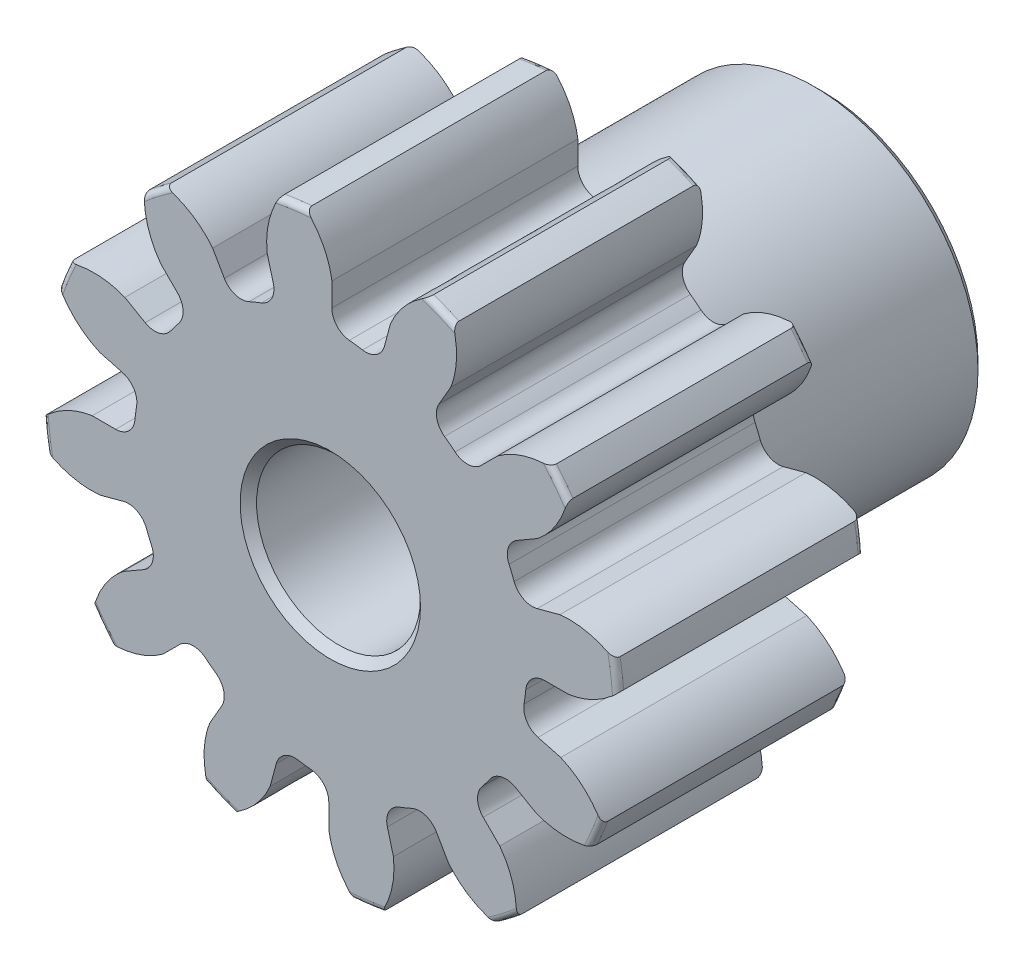
SolidWorks part; units mm, degrees
ref_plane "Front" through (0, 0, 0) normal (0, 0, 1) x (1, 0, 0)
ref_plane "Top" through (0, 0, 0) normal (0, 1, 0) x (1, 0, 0)
ref_plane "Right" through (0, 0, 0) normal (1, 0, 0) x (0, 0, -1)
sketch "Sketch1" plane through (0, 0, 0) normal (0, 0, 1) x (1, 0, 0)
  line L0 (-152.4, 0) -> (152.4, 0) construction
  circle A0 centre (0, 0) radius 5.588
  circle A1 centre (0, 0) radius 4.7625 construction
  circle A3 centre (0, 0) radius 3.8021 construction
  dimension "D1" = 1.7859
  dimension "OD" = 11.176
  dimension "Ptich Dia" = 9.525
  dimension "Root Dia" = 7.6041
  dimension "D3" = 0.8255
  dimension "Number of Teeth" = 304.8
extrude "Boss-Extrude1" add sketch "Sketch1" against normal blind 4.7625
sketch "Sketch2" plane through (0, 0, 0) normal (1, 0, 0) x (0, 0, -1)
  line L0 (4.7625, 0) -> (9.525, 0)
  line L1 (4.7625, 0) -> (4.7625, 3.175)
  line L2 (4.7625, 3.175) -> (9.525, 3.175)
  line L3 (9.525, 3.175) -> (9.525, 0)
  point P5 (9.525, -3.175)
  point P6 (0, -5.588)
  point P7 (4.7625, -5.588)
  point P9 (0, 5.588)
  dimension "Face Wd" = 4.7625
  dimension "B Hub Dia" = 6.35
  dimension "D O'all Lg." = 9.525
revolve "Revolve1" add sketch "Sketch2" angle 360 about L0
fillet "Fillet2" radius 0.1118 3 edges at (5.588, 0, -4.7625) (5.588, 0, 0) (3.175, 0, -4.7625)
sketch "Sketch3" plane through (0, 0, 0) normal (0, 0, 1) x (1, 0, 0)
  line L0 (0, 0) -> (0, 5.588) construction
  line L1 (-1.1545, 4.4639) -> (0, 4.7625)
  line L2 (-9.5921, 4.7625) -> (9.5921, 4.7625) construction
  line L3 (-9.2865, 2.3608) -> (9.2865, 7.1642) construction
  line L4 (-1.1545, 4.4639) -> (0, 0) construction
  line L5 (-2.9446, 3.5481) -> (0, 0) construction
  line L6 (-2.9446, 3.5481) -> (-0.4867, 5.588) construction
  line L7 (-0.805, 4.54) -> (0, 0) construction
  line L8 (-0.805, 4.54) -> (0.0169, 4.6857) construction
  arc A0 (-1.1545, 4.4639) -> (-2.9446, 3.5481) centre (0, 0) ccw
  circle A1 centre (0, 0) radius 4.7625 construction
  circle A2 centre (0, 0) radius 4.6108 construction
  arc A3 (-1.1545, 4.4639) -> (-0.805, 4.54) centre (0, 0) cw
  circle A4 centre (0, 0) radius 5.588 construction
  point P6 (0, 4.7625)
  dimension "D1" = 1.1924
  dimension "Pressure Angle" = 14.5
  dimension "D2" = 2.0271
  dimension "D3" = 3.1942
  dimension "D4" = 0.3577
  dimension "D5" = 0.8347
sketch "Sketch4" plane through (0, 0, 0) normal (0, 0, 1) x (1, 0, 0)
  line L0 (0, 0) -> (0.6163, 4.6814) construction
  line L1 (0.0297, 4.6107) -> (0.0297, 3.8019)
  line L2 (0, 4.7625) -> (1.2326, 4.6002) construction
  line L3 (1.1646, 4.4613) -> (0.9553, 3.6801)
  line L4 (0.0297, 3.8019) -> (0, 0) construction
  line L5 (0, 0) -> (0, 5.588) construction
  line L6 (-2.9446, 3.5481) -> (-0.4867, 5.588) construction
  line L7 (-2.9446, 3.5481) -> (-0.4867, 5.588) construction
  arc A0 (0.9553, 3.6801) -> (0.0297, 3.8019) centre (0, 0) ccw
  arc A1 (0, 4.7625) -> (1.2326, 4.6002) centre (0, 0) cw construction
  circle A2 centre (0, 0) radius 4.7625 construction
  circle A3 centre (0, 0) radius 4.6108 construction
  circle A4 centre (0, 0) radius 3.8021 construction
  arc A5 (1.9164, 5.2716) -> (-0.4867, 5.588) centre (0, 0) ccw
  spline S0 degree 2 poles (-0.4867, 5.588) (-0.0518, 5.1617) (0.0297, 4.6107) knots 0 0 0 1 1 1
  spline S1 degree 2 poles (1.9164, 5.2716) (1.386, 4.9724) (1.1646, 4.4613) knots 0 0 0 1 1 1
  dimension "D1" = 1.2468
extrude "Cut-Extrude1" cut sketch "Sketch4" against normal through all
fillet "Fillet1" radius 0.374 2 edges at (0.9553, 3.6801, -2.3813) (0.0297, 3.8019, -2.3813)
pattern_circular "CirPattern1" count 12 over 360 about axis through (0, 0, -4.7625) along (0, 0, 1) of "Cut-Extrude1", "Fillet1"
sketch "Sketch5" plane through (0, 0, 0) normal (0, 0, 1) x (1, 0, 0)
  circle A0 centre (0, 0) radius 1.5875
  circle A1 centre (0, 0) radius 1.5875 construction
  dimension "Bore Min" = 3.175
  dimension "Bore Max" = 3.175
extrude "Cut-Extrude2" cut sketch "Sketch5" against normal through all
chamfer "Chamfer1" distance 0.1588 angle 45 3 edges at (3.175, 0, -9.525) (1.5875, 0, 0) (1.5875, 0, -9.525)
sketch "Pitch Dia" plane through (0, 0, 0) normal (0, 0, 1) x (1, 0, 0)
  circle A0 centre (0, 0) radius 4.7625 construction
  circle A1 centre (0, 0) radius 4.7625 construction
equation "\"D1@Boss-Extrude1\" = \"Face Wd@Sketch2\""
equation "\"D2@Sketch3\" = \"D1@Sketch3\"*1.7"
equation "\"D3@Sketch3\" = \"D1@Sketch3\"+\"D2@Sketch3\"-.001"
equation "\"D4@Sketch3\" = \"D1@Sketch3\"*.3"
equation "\"D5@Sketch3\" = \"D1@Sketch3\"-\"D4@Sketch3\""
equation "\"D1@Sketch4\" = 1.5708/(\"Number of Teeth@Sketch1\"/\"Ptich Dia@Sketch1\")"
equation "\"D1@Chamfer1\" = \"B Hub Dia@Sketch2\"*.025"
equation "\"D1@CirPattern1\" = \"Number of Teeth@Sketch1\""
equation "\"D1@Fillet1\" = \"D1@Sketch4\"*.3"
equation "\"D1@Fillet2\" = \"OD@Sketch1\"*.01"
equation "\"D1@Sketch1\" = 2.250/(\"Number of Teeth@Sketch1\"/\"Ptich Dia@Sketch1\")"
